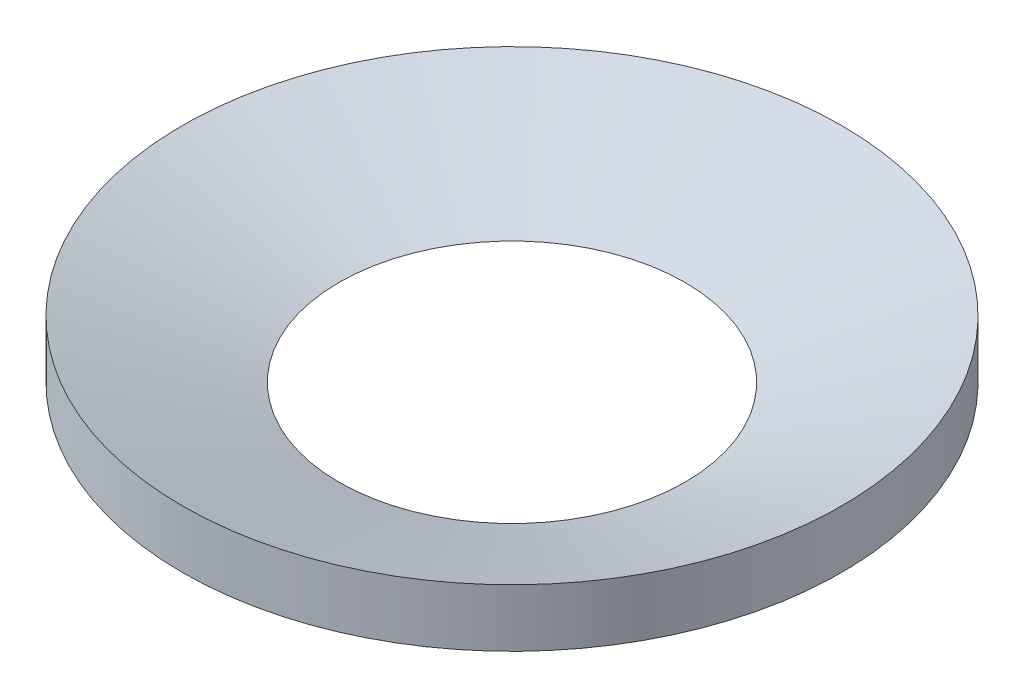
SolidWorks part; units mm, degrees
ref_plane "Front Plane" through (0, 0, 0) normal (0, 0, 1) x (1, 0, 0)
ref_plane "Top Plane" through (0, 0, 0) normal (0, 1, 0) x (1, 0, 0)
ref_plane "Right Plane" through (0, 0, 0) normal (1, 0, 0) x (0, 0, -1)
sketch "Sketch1" plane through (0, 0, 0) normal (0, 0, 1) x (1, 0, 0)
  line L0 (10.5, 0) -> (20, 0)
  line L1 (20, 0) -> (20, 3.5)
  line L2 (20, 3.5) -> (10.5, 0)
  line L3 (0, 0) -> (20, 3.5) construction
  line L4 (0, 0) -> (0, 34.907) construction
  dimension "D1" = 10.5
  dimension "D2" = 20
  dimension "D3" = 3.5
  dimension "D4" = 80.074
revolve "Revolve1" add sketch "Sketch1" angle 360 about L4
